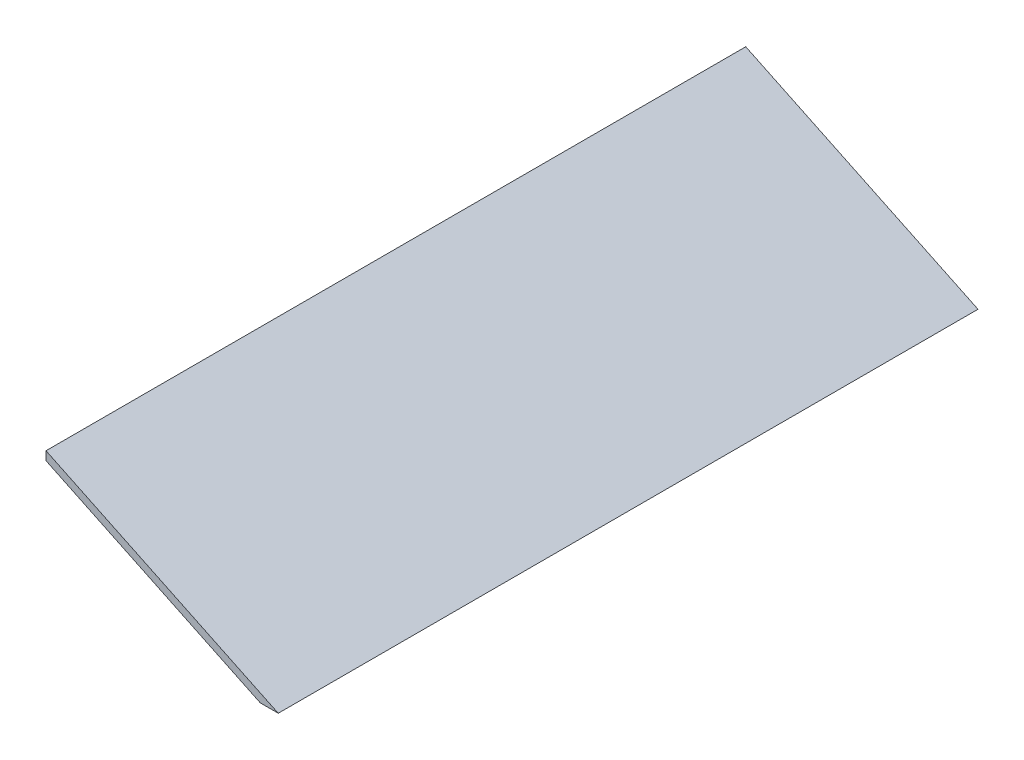
SolidWorks part; units mm, degrees
ref_plane "Ebene vorne" through (0, 0, 0) normal (0, 0, 1) x (1, 0, 0)
ref_plane "Ebene oben" through (0, 0, 0) normal (0, 1, 0) x (1, 0, 0)
ref_plane "Ebene rechts" through (0, 0, 0) normal (1, 0, 0) x (0, 0, -1)
sketch "Skizze1" plane through (0, 0, 0) normal (0, 0, 1) x (1, 0, 0)
  line L0 (-331.8608, 76.5249) -> (-331.8608, 70.9811)
  line L1 (-182.5, 5) -> (-194.0766, 5)
  line L12 (-331.8608, 76.5249) -> (-182.5, 5)
  line L23 (-331.8608, 70.9811) -> (-194.0766, 5)
extrude "Aufsatz-Linear austragen1" add sketch "Skizze1" along normal blind 450
